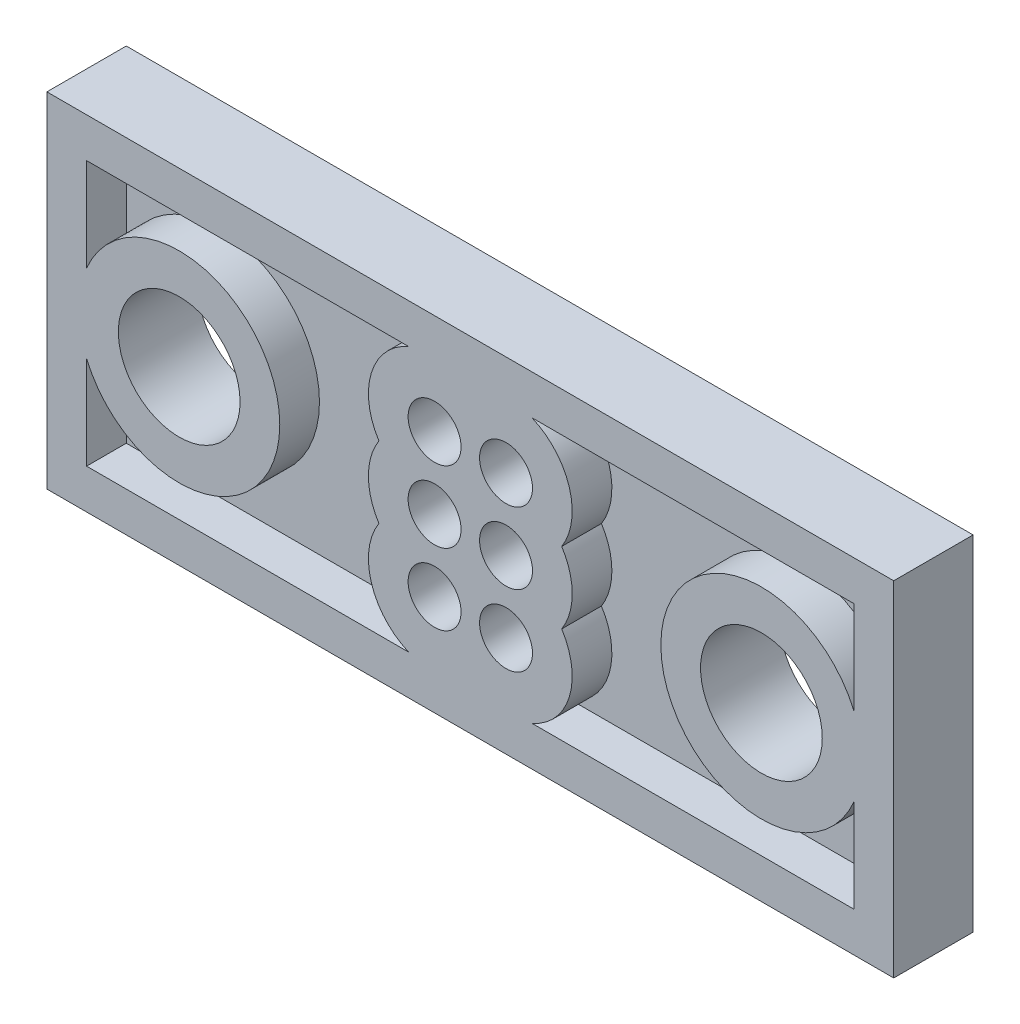
SolidWorks part; units mm, degrees
other "Objet de détail1"
ref_plane "Face" through (0, 0, 0) normal (0, 0, 1) x (1, 0, 0)
ref_plane "Dessus" through (0, 0, 0) normal (0, 1, 0) x (1, 0, 0)
ref_plane "Droite" through (0, 0, 0) normal (1, 0, 0) x (0, 0, -1)
sketch "Esquisse1" plane through (0, 0, 0) normal (0, 0, 1) x (1, 0, 0)
  line L0 (0, 6.5) -> (5, 6.5) construction
  line L1 (0, 0) -> (32, 0)
  line L2 (0, 0) -> (0, 13)
  line L3 (0, 13) -> (32, 13)
  line L4 (32, 0) -> (32, 13)
  line L5 (32, 6.5) -> (27, 6.5) construction
  line L6 (16, 13) -> (16, 0) construction
  line L7 (5, 6.5) -> (27, 6.5) construction
  circle A0 centre (5, 6.5) radius 2.3
  circle A1 centre (27, 6.5) radius 2.3
  circle A2 centre (14.65, 9.2) radius 1
  circle A3 centre (17.35, 9.2) radius 1
  circle A4 centre (17.35, 6.5) radius 1
  circle A6 centre (14.65, 3.8) radius 1
  circle A7 centre (14.65, 6.5) radius 1
  circle A8 centre (17.35, 3.8) radius 1
  dimension "D5" = 4.6
  dimension "D12" = 2.7
  dimension "D13" = 2
  dimension "D14" = 2
  dimension "D15" = 2
  dimension "D16" = 2
  dimension "D17" = 2
  dimension "D18" = 2
  dimension "D1" = 32
  dimension "D2" = 13
  dimension "D3" = 5
  dimension "D4" = 5
  dimension "D8" = 2.7
  dimension "D10" = 2.7
  dimension "D11" = 2.7
  dimension "D19" = 2.7
  dimension "D20" = 1.35
extrude "Boss.-Extru.1" add sketch "Esquisse1" along normal blind 3
sketch "Esquisse2" plane through (0, 0, 3) normal (0, 0, 1) x (1, 0, 0)
  line L0 (16, 13) -> (16, 0) construction
  line L1 (32, 13) -> (0, 13) construction
  line L2 (0, 0) -> (32, 0) construction
  line L3 (1.5, 11.5) -> (13.6702, 11.5)
  line L4 (0, 13) -> (0, 0) construction
  line L5 (0, 6.5) -> (16, 6.5) construction
  line L10 (1.5, 11.5) -> (1.5, 7.9799)
  line L11 (1.5, 1.5) -> (1.5, 5.0201)
  line L12 (1.5, 1.5) -> (13.6702, 1.5)
  line L13 (30.5, 1.5) -> (18.3298, 1.5)
  line L14 (30.5, 1.5) -> (30.5, 5.0201)
  line L15 (30.5, 11.5) -> (30.5, 7.9799)
  line L16 (30.5, 11.5) -> (18.3298, 11.5)
  arc A1 (1.5, 5.0201) -> (1.5, 7.9799) centre (5, 6.5) ccw
  circle A2 centre (5, 6.5) radius 2.3 construction
  circle A10 centre (14.65, 9.2) radius 2.5
  arc A11 (13.6702, 11.5) -> (12.5458, 7.85) centre (14.65, 9.2) ccw
  arc A15 (13.6702, 1.5) -> (12.5458, 5.15) centre (14.65, 3.8) cw
  circle A16 centre (14.65, 6.5) radius 2.5
  arc A17 (12.5458, 7.85) -> (12.5458, 5.15) centre (14.65, 6.5) ccw
  arc A18 (19.4542, 7.85) -> (19.4542, 5.15) centre (17.35, 6.5) cw
  arc A19 (18.3298, 1.5) -> (19.4542, 5.15) centre (17.35, 3.8) ccw
  arc A20 (18.3298, 11.5) -> (19.4542, 7.85) centre (17.35, 9.2) cw
  arc A21 (30.5, 5.0201) -> (30.5, 7.9799) centre (27, 6.5) cw
  dimension "D1" = 1.5
  dimension "D2" = 1.5
  dimension "D3" = 1.5
  dimension "D4" = 1.5
  dimension "D5" = 1.5
extrude "Enlèv. mat.-Extru.1" cut sketch "Esquisse2" against normal blind 1.5
